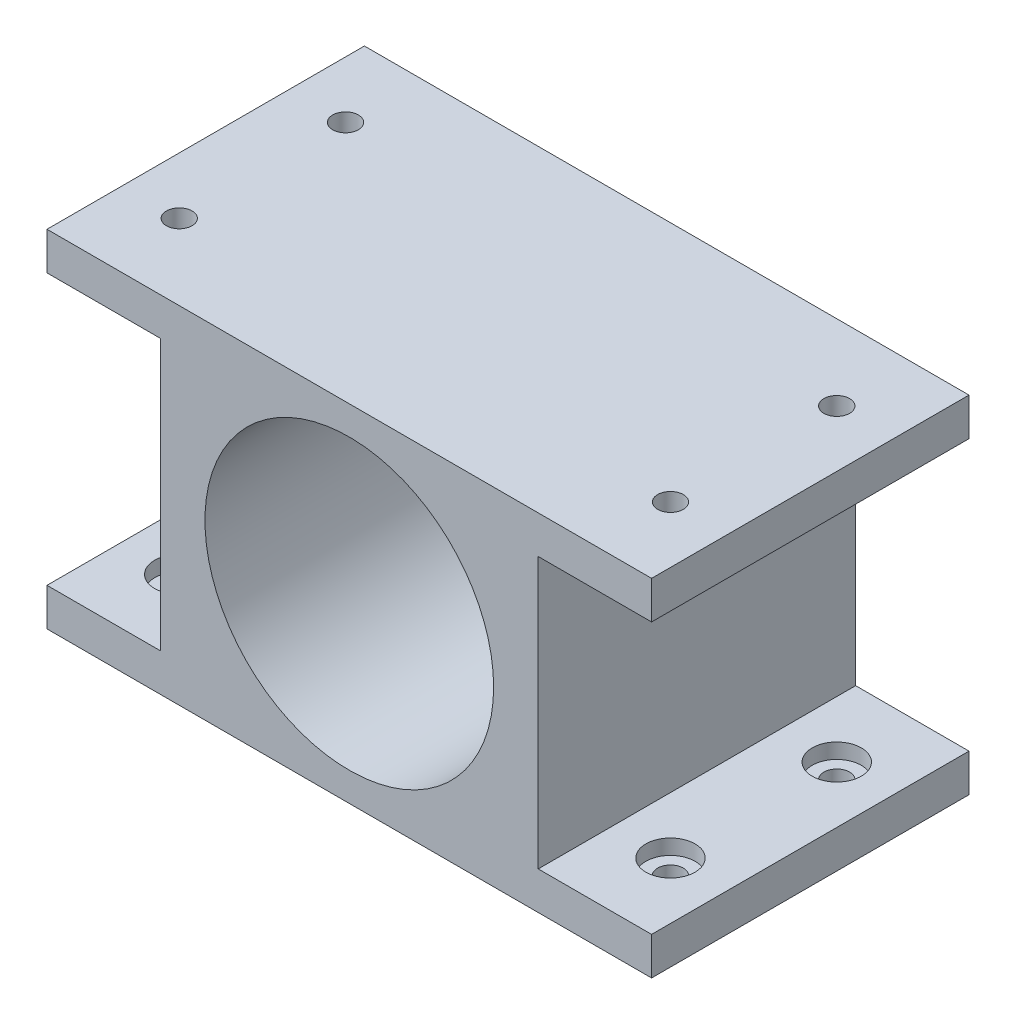
SolidWorks part; units mm, degrees
ref_plane "Plan de face" through (0, 0, 0) normal (0, 0, 1) x (1, 0, 0)
ref_plane "Plan de dessus" through (0, 0, 0) normal (0, 1, 0) x (1, 0, 0)
ref_plane "Plan de droite" through (0, 0, 0) normal (1, 0, 0) x (0, 0, -1)
sketch "Esquisse1" plane through (0, 0, 0) normal (0, 0, 1) x (1, 0, 0)
  line L0 (25, 22.9) -> (25, 42.1) construction
  line L1 (0, 0) -> (50, 0)
  line L2 (0, 0) -> (0, 45.8)
  line L3 (0, 45.8) -> (50, 45.8)
  line L4 (50, 0) -> (50, 45.8)
  line L5 (50, 0) -> (65, 0)
  line L6 (50, 0) -> (50, 5)
  line L7 (50, 5) -> (65, 5)
  line L8 (65, 0) -> (65, 5)
  line L9 (0, 0) -> (-15, 0)
  line L10 (0, 0) -> (0, 5)
  line L11 (0, 5) -> (-15, 5)
  line L12 (-15, 0) -> (-15, 5)
  line L13 (41.6277, 13.3) -> (25, 22.9) construction
  line L14 (25, 22.9) -> (8.3723, 13.3) construction
  line L15 (5.456, 22.9632) -> (43.856, 22.9632) construction
  line L16 (0, 45.8) -> (-15, 45.8)
  line L17 (0, 45.8) -> (0, 40.8)
  line L18 (0, 40.8) -> (-15, 40.8)
  line L19 (-15, 45.8) -> (-15, 40.8)
  line L20 (50, 45.8) -> (65, 45.8)
  line L21 (50, 45.8) -> (50, 40.8)
  line L22 (50, 40.8) -> (65, 40.8)
  line L23 (65, 45.8) -> (65, 40.8)
  circle A0 centre (25, 22.9) radius 19.2
  circle A1 centre (25, 38.1) radius 2
  circle A2 centre (38.1636, 15.3) radius 2
  circle A3 centre (11.8364, 15.3) radius 2
  circle A4 centre (25, 22.9) radius 11
  dimension "D5" = 38.4
  dimension "D12" = 4
  dimension "D13" = 4
  dimension "D14" = 4
  dimension "D22" = 22
  dimension "D1" = 45.8
  dimension "D2" = 50
  dimension "D3" = 22.9
  dimension "D4" = 25
  dimension "D6" = 5
  dimension "D7" = 15
  dimension "D8" = 15
  dimension "D9" = 5
  dimension "D10" = 120
  dimension "D11" = 120
  dimension "D15" = 4
  dimension "D16" = 4
  dimension "D17" = 4
  dimension "D18" = 5
  dimension "D19" = 15
  dimension "D20" = 5
  dimension "D21" = 15
  dimension "D23" = 38.4
extrude "Boss.-Extru.1" add sketch "Esquisse1" along normal blind 2 contours L16 L19 L18 L2 | L1 L4 L3 L2 A0 | L12 L9 L2 L11 | L5 L8 L7 L4 | L23 L20 L4 L22 | A0 A3 A2 A1
sketch "Esquisse3" plane through (0, 0, 2) normal (0, 0, 1) x (1, 0, 0)
  line L0 (0, 40.8) -> (50, 5)
  line L1 (50, 40.8) -> (0, 5)
  line L12 (65, 45.8) -> (-15, 45.8)
  line L13 (-15, 45.8) -> (-15, 40.8)
  line L14 (-15, 40.8) -> (0, 40.8)
  line L15 (0, 40.8) -> (0, 5)
  line L16 (0, 5) -> (-15, 5)
  line L17 (-15, 5) -> (-15, 0)
  line L18 (-15, 0) -> (65, 0)
  line L19 (65, 0) -> (65, 5)
  line L20 (65, 5) -> (50, 5)
  line L21 (50, 5) -> (50, 40.8)
  line L22 (50, 40.8) -> (65, 40.8)
  line L23 (65, 40.8) -> (65, 45.8)
  line L24 (65, 45.8) -> (-15, 45.8)
  line L25 (-15, 45.8) -> (-15, 40.8)
  line L26 (-15, 40.8) -> (0, 40.8)
  line L27 (0, 40.8) -> (0, 5)
  line L28 (0, 5) -> (-15, 5)
  line L29 (-15, 5) -> (-15, 0)
  line L30 (-15, 0) -> (65, 0)
  line L31 (65, 0) -> (65, 5)
  line L32 (65, 5) -> (50, 5)
  line L33 (50, 5) -> (50, 40.8)
  line L34 (50, 40.8) -> (65, 40.8)
  line L35 (65, 40.8) -> (65, 45.8)
  circle A0 centre (25, 22.9) radius 19.1
  line M13 (65, 45.8) -> (-15, 45.8)
  line M14 (-15, 45.8) -> (-15, 40.8)
  line M15 (-15, 40.8) -> (0, 40.8)
  line M16 (0, 40.8) -> (0, 5)
  line M17 (0, 5) -> (-15, 5)
  line M18 (-15, 5) -> (-15, 0)
  line M19 (-15, 0) -> (65, 0)
  line M20 (65, 0) -> (65, 5)
  line M21 (65, 5) -> (50, 5)
  line M22 (50, 5) -> (50, 40.8)
  line M23 (50, 40.8) -> (65, 40.8)
  line M24 (65, 40.8) -> (65, 45.8)
  dimension "D2" = 38.2
  dimension "D1" = 0
extrude "Boss.-Extru.2" add sketch "Esquisse3" along normal blind 40 contours A0 L1 L0 M23 M24 M13 M14 M15 | A0 L0 L1 M16 | A0 L1 L0 M17 M18 M19 M20 M21 | A0 L0 L1 M22
sketch "Esquisse4" plane through (0, 5, 0) normal (0, 1, 0) x (1, 0, 0)
  line L0 (65, 0) -> (50, 0) construction
  line L1 (50, 0) -> (50, -42) construction
  line L2 (50, -42) -> (65, -42) construction
  line L3 (65, -42) -> (65, 0) construction
  line L4 (0, 0) -> (-15, 0) construction
  line L5 (-15, 0) -> (-15, -42) construction
  line L6 (-15, -42) -> (0, -42) construction
  line L7 (0, -42) -> (0, 0) construction
  line L8 (65, 0) -> (50, 0)
  line L9 (50, 0) -> (50, -42)
  line L10 (50, -42) -> (65, -42)
  line L11 (65, -42) -> (65, 0)
  line L12 (0, 0) -> (-15, 0)
  line L13 (-15, 0) -> (-15, -42)
  line L14 (-15, -42) -> (0, -42)
  line L15 (0, -42) -> (0, 0)
  line L16 (-7.5, -42) -> (-7.5, 0)
  line L17 (-7.5, 0) -> (57.5, 0)
  line L18 (57.5, 0) -> (57.5, -42)
  line L23 (0, 0) -> (-15, 0)
  line L24 (0, -42) -> (0, 0)
  line L25 (-15, -42) -> (0, -42)
  line L26 (-15, 0) -> (-15, -42)
  line L27 (0, 0) -> (-15, 0)
  line L28 (0, -42) -> (0, 0)
  line L29 (-15, -42) -> (0, -42)
  line L30 (-15, 0) -> (-15, -42)
  point P10 (-7.5, -32)
  point P12 (-7.5, -10)
  point P14 (57.5, -10)
  point P15 (57.5, -32)
  dimension "D1" = 10
  dimension "D2" = 10
  dimension "D3" = 10
  dimension "D4" = 10
  dimension "D5" = 0
hole_wizard "Chambrage pour vis à tête cylindrique à 6 pans creux (ou vis CHC) M31" positions "Esquisse3D1" profile "Esquisse6" counterbore size "M3" standard "Ansi Metric"
sketch3d "Esquisse3D1"
  point P0 (57.5, 5, 32)
  point P3 (57.5, 5, 10)
  point P6 (-7.5, 5, 10)
  point P9 (-7.5, 5, 32)
sketch "Esquisse6" plane through (57.5, 5, 32) normal (1, 0, 0) x (0, 0, 1)
  line L0 (0, 0) -> (0, 5)
  line L1 (0, 5) -> (1.7, 5)
  line L3 (1.7, 5) -> (1.7, 2)
  line L4 (1.7, 2) -> (3.25, 2)
  line L5 (3.25, 2) -> (3.25, 0)
  line L7 (3.25, 0) -> (0, 0)
  line L11 (0, -6.35) -> (0, 107.95) construction
  dimension "Diamètre du perçage jusqu'au prochain" = 3.4
  dimension "Profondeur du perçage jusqu'au prochain" = 5
  dimension "Diamètre du chambrage" = 6.5
  dimension "Profondeur du chambrage" = 2
ref_plane "Plan1" through (0, 22.9, 0) normal (0, 1, 0) x (1, 0, 0)
mirror "Symétrie1" about plane through (0, 22.9, 0) normal (0, 1, 0) of "Chambrage pour vis à tête cylindrique à 6 pans creux (ou vis CHC) M31"
